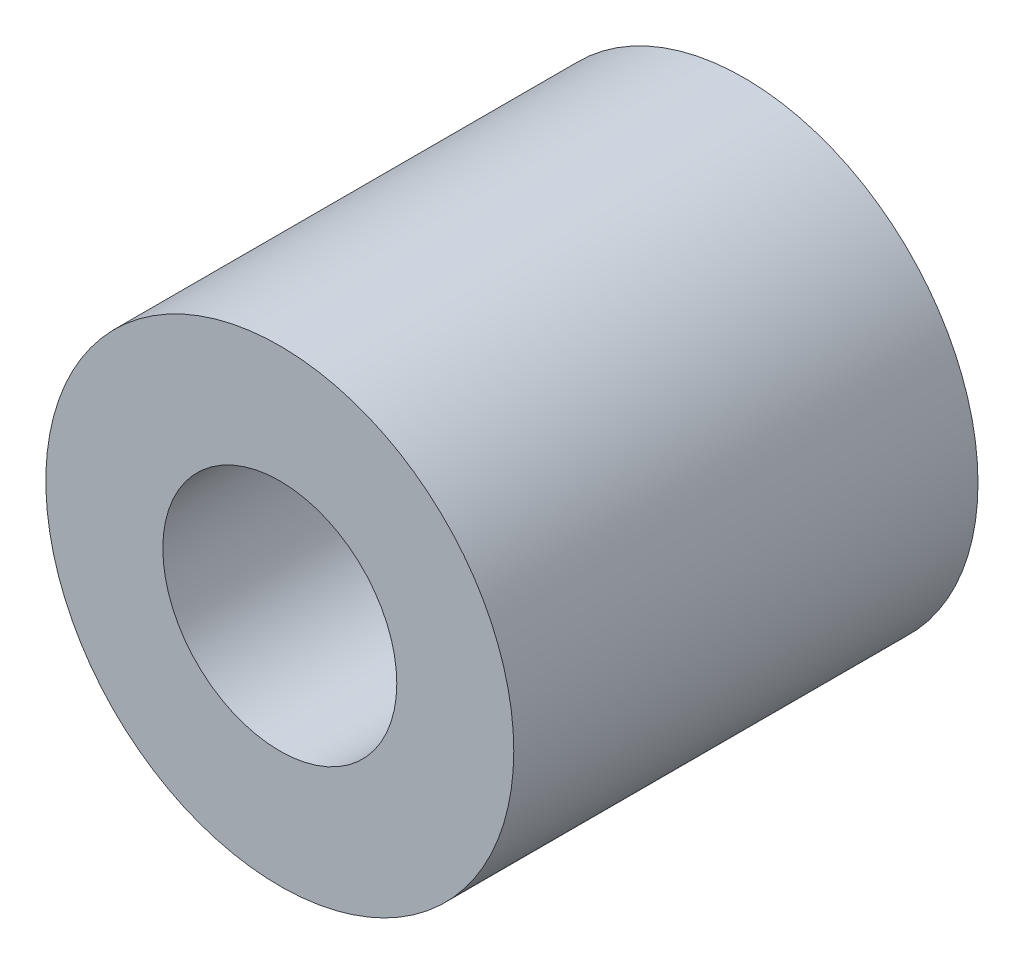
SolidWorks part; units mm, degrees
material "841 Oilite Bronze"
ref_plane "Front Plane" through (0, 0, 0) normal (0, 0, 1) x (1, 0, 0)
ref_plane "Top Plane" through (0, 0, 0) normal (0, 1, 0) x (1, 0, 0)
ref_plane "Right Plane" through (0, 0, 0) normal (1, 0, 0) x (0, 0, -1)
sketch "Sketch1" plane through (0, 0, 0) normal (0, 0, 1) x (1, 0, 0)
  circle A0 centre (0, 0) radius 3.2004
  circle A1 centre (0, 0) radius 1.6002
  dimension "OD" = 6.4008
  dimension "ID" = 3.2004
sketch "Sketch2" plane through (0, 0, 0) normal (1, 0, 0) x (0, 0, -1)
  line L2 (3.175, 0) -> (-3.175, 0) construction
  line L4 (-3.175, -3.2004) -> (-3.175, 3.2004) construction
  line L5 (-3.175, -1.6002) -> (3.175, -1.6002)
  line L6 (3.175, 1.6002) -> (-3.175, 1.6002)
  line L7 (3.175, -3.2004) -> (3.175, 3.2004) construction
  line L8 (-3.175, 3.2004) -> (3.175, 3.2004) construction
  line L9 (-3.175, -3.2004) -> (3.175, -3.2004) construction
  line L10 (0, 3.2004) -> (0, -3.2004) construction
  line L11 (0, 1.6002) -> (0, -1.6002) construction
  point P4 (0, -1.6002)
  point P7 (0, 1.6002)
  point P8 (0, 0)
  point P12 (-3.175, 0)
  point P15 (3.175, 0)
  point P16 (0, -3.2004)
  point P17 (0, 3.2004)
  dimension "Length" = 6.35
sketch "Sketch5" plane through (0, 0, 0) normal (0, 0, 1) x (1, 0, 0)
  circle A1 centre (0, 0) radius 1.6002
  circle A2 centre (0, 0) radius 1.6002
  circle A3 centre (0, 0) radius 3.2004
  circle A4 centre (0, 0) radius 3.2004
  dimension "D1" = 0
  dimension "D2" = 0
extrude "Boss-Extrude1" add sketch "Sketch5" along normal up to vertex (3.175 mm away) and the other way up to vertex (3.175 mm away) up to point (0, 0, 3.175) other way up to point (0, 0, -3.175)
sketch "Sketch4" plane through (0, 0, 3.175) normal (0, 0, 1) x (1, 0, 0)
  line L0 (0, 0) -> (-1.1315, 1.1315)
  line L2 (0, -3.2004) -> (0, 3.2004) construction
  circle A1 centre (0, 0) radius 1.6002 construction
  dimension "D1" = 45
equation "\"D1\"= \"Length@Sketch2\""
